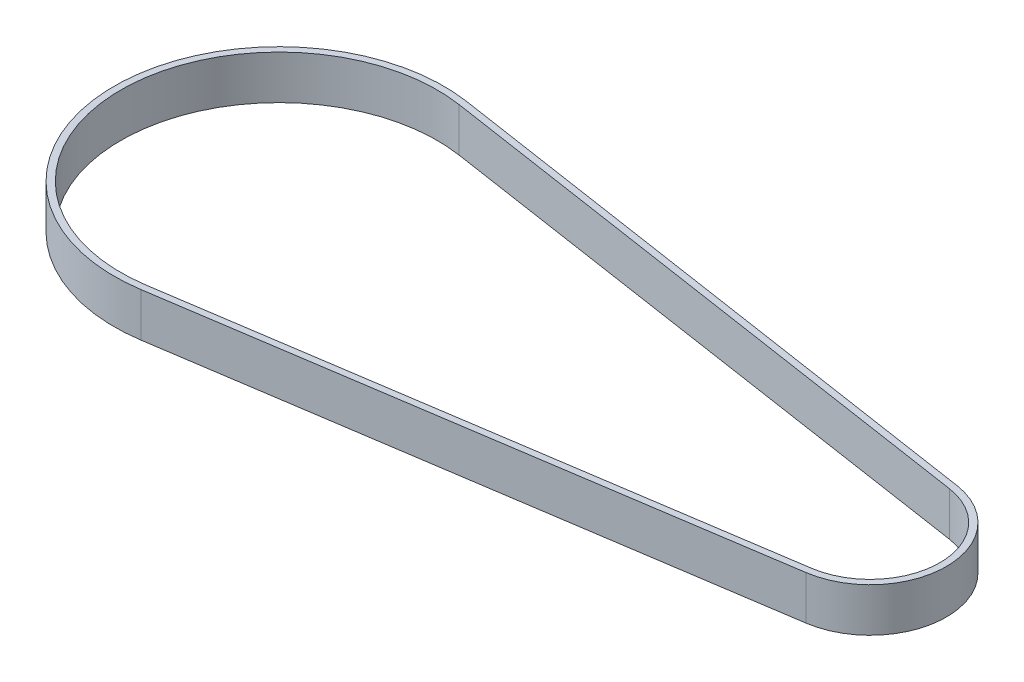
SolidWorks part; units mm, degrees
material "BUTYL"
ref_plane "Front Plane" through (0, 0, 0) normal (0, 0, 1) x (1, 0, 0)
ref_plane "Top Plane" through (0, 0, 0) normal (0, 1, 0) x (1, 0, 0)
ref_plane "Right Plane" through (0, 0, 0) normal (1, 0, 0) x (0, 0, -1)
sketch "Sketch1" plane through (0, 0, 0) normal (0, 1, 0) x (1, 0, 0)
  line L0 (-68.5794, 35.7179) -> (63.3951, 15.7357)
  line L1 (-68.5794, -35.7179) -> (63.3951, -15.7357)
  line L2 (-68.3548, 37.201) -> (63.6197, 17.2187)
  line L3 (-68.3548, -37.201) -> (63.6197, -17.2187)
  arc A0 (-68.5794, 35.7179) -> (-68.5794, -35.7179) centre (-73.9874, 0) ccw
  arc A1 (63.3951, -15.7357) -> (63.3951, 15.7357) centre (61.0126, 0) ccw
  arc A2 (63.6197, -17.2187) -> (63.6197, 17.2187) centre (61.0126, 0) ccw
  arc A3 (-68.3548, 37.201) -> (-68.3548, -37.201) centre (-73.9874, 0) ccw
  dimension "D2" = 72.25
  dimension "D3" = 31.83
  dimension "D1" = 135
  dimension "D4" = 1.5
extrude "Boss-Extrude1" add sketch "Sketch1" along normal blind 10
